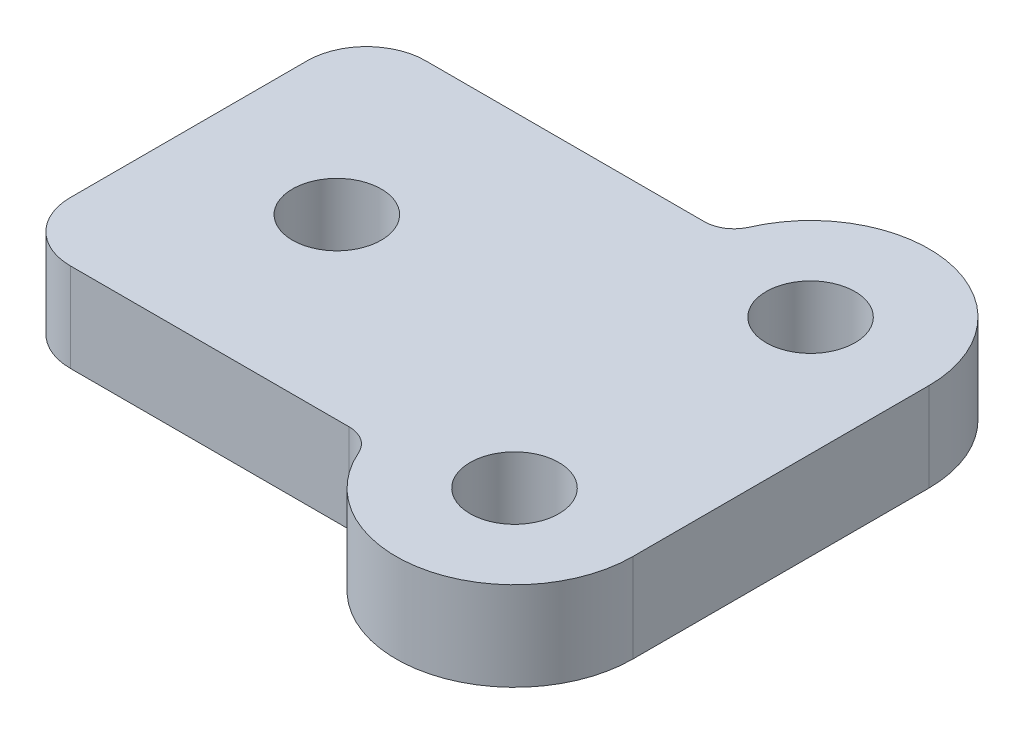
SolidWorks part; units mm, degrees
ref_plane "Front Plane" through (0, 0, 0) normal (0, 0, 1) x (1, 0, 0)
ref_plane "Top Plane" through (0, 0, 0) normal (0, 1, 0) x (1, 0, 0)
ref_plane "Right Plane" through (0, 0, 0) normal (1, 0, 0) x (0, 0, -1)
sketch "Sketch1" plane through (0, 0, 0) normal (0, 1, 0) x (1, 0, 0)
  line L7 (15, 5) -> (15, -5)
  line L14 (-5, 4) -> (-5, -4)
  line L15 (-3, 6) -> (6.4174, 6)
  line L16 (-3, -6) -> (6.4174, -6)
  circle A0 centre (0, 0) radius 1.5
  arc A2 (15, 5) -> (7.3339, 6.6) centre (11, 5) ccw
  circle A3 centre (11, 5) radius 1.5
  circle A4 centre (11, -5) radius 1.5
  arc A5 (7.3339, -6.6) -> (15, -5) centre (11, -5) ccw
  arc A6 (-3, 6) -> (-5, 4) centre (-3, 4) ccw
  arc A7 (-5, -4) -> (-3, -6) centre (-3, -4) ccw
  arc A8 (6.4174, 6) -> (7.3339, 6.6) centre (6.4174, 7) ccw
  arc A9 (7.3339, -6.6) -> (6.4174, -6) centre (6.4174, -7) ccw
  point P4 (0, 0)
  point P6 (9.9222, -1.1983)
  point P22 (-24.1144, -0.2247)
  point P28 (6.8874, 7.8437)
  point P32 (6.8874, -7.7303)
  dimension "D1" = 3
  dimension "D9" = 10
  dimension "D10" = 8
  dimension "D11" = 4
  dimension "D2" = 5
  dimension "D6" = 3
  dimension "D7" = 3
  dimension "D8" = 8
  dimension "D12" = 4
  dimension "D13" = 1
  dimension "D14" = 1
  dimension "D15" = 5
  dimension "D17" = 5
  dimension "D3" = 15
  dimension "D4" = 8
  dimension "D5" = 11
  dimension "D16" = 11
  dimension "D19" = 20
  dimension "D20" = 10.3339
  dimension "D21" = 0.9165
extrude "Boss-Extrude1" add sketch "Sketch1" along normal blind 3
